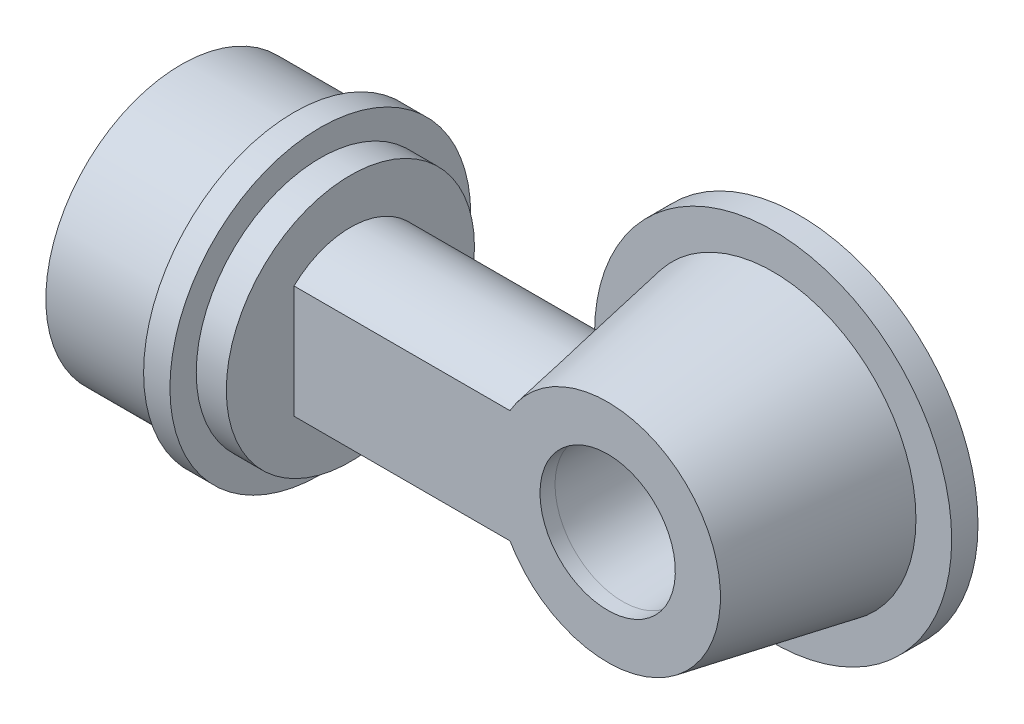
SolidWorks part; units mm, degrees
ref_plane "Front Plane" through (0, 0, 0) normal (0, 0, 1) x (1, 0, 0)
ref_plane "Top Plane" through (0, 0, 0) normal (0, 1, 0) x (1, 0, 0)
ref_plane "Right Plane" through (0, 0, 0) normal (1, 0, 0) x (0, 0, -1)
sketch "Croquis1" plane through (0, 0, 0) normal (1, 0, 0) x (0, 0, -1)
  circle A0 centre (0, 0) radius 18
  circle A1 centre (0, 0) radius 15.5
  dimension "D1" = 36
  dimension "D2" = 2.5
extrude "Saliente-Extruir1" add sketch "Croquis1" along normal blind 15
sketch "Croquis2" plane through (15, 0, 0) normal (1, 0, 0) x (0, 0, -1)
  circle A0 centre (0, 0) radius 20
  circle A1 centre (0, 0) radius 15.5
  circle A2 centre (0, 0) radius 15.5 construction
  dimension "D1" = 40
extrude "Saliente-Extruir2" add sketch "Croquis2" along normal blind 3.5
sketch "Croquis4" plane through (18.5, 0, 0) normal (1, 0, 0) x (0, 0, -1)
  circle A0 centre (0, 0) radius 16.5
  circle A1 centre (0, 0) radius 13.5
  dimension "D1" = 33
  dimension "D2" = 3
extrude "Saliente-Extruir3" add sketch "Croquis4" along normal blind 4
sketch "Croquis5" plane through (22.5, 0, 0) normal (1, 0, 0) x (0, 0, -1)
  circle A0 centre (0, 0) radius 16.5
  circle A1 centre (0, 0) radius 16.5 construction
extrude "Saliente-Extruir4" add sketch "Croquis5" against normal blind 3
sketch "Croquis6" plane through (22.5, 0, 0) normal (1, 0, 0) x (0, 0, -1)
  line L0 (0, 10.5) -> (0, 7.5) construction
  line L4 (-7.5, 7.5) -> (-7.5, -7.5)
  line L6 (7.5, 7.5) -> (7.5, -7.5)
  line L7 (-7.5, 7.5) -> (7.5, -7.5) construction
  line L8 (-7.5, -7.5) -> (7.5, 7.5) construction
  line L9 (0, -7.5) -> (0, -10.5) construction
  line L10 (-5.5, 6.5903) -> (-5.5, -6.5903)
  line L11 (5.5, 6.5903) -> (5.5, -6.5903)
  arc A2 (-7.5, 7.5) -> (7.5, 7.5) centre (0, -0.375) cw
  arc A3 (-7.5, -7.5) -> (7.5, -7.5) centre (0, 0.375) ccw
  arc A4 (-5.5, -6.5903) -> (5.5, -6.5903) centre (0, 0.375) ccw
  arc A5 (-5.5, 6.5903) -> (5.5, 6.5903) centre (0, -0.375) cw
  point P0 (0, 0)
  dimension "D1" = 15
  dimension "D2" = 15
  dimension "D3" = 21
  dimension "D4" = 10.5
  dimension "D5" = 2
extrude "Saliente-Extruir5" add sketch "Croquis6" along normal blind 31
sketch "Croquis7" plane through (0, 0, 7.5) normal (0, 0, 1) x (1, 0, 0)
  line L0 (53.5, 0) -> (77.2121, 0) construction
  line L1 (53.5, 7.5) -> (53.5, -7.5) construction
  circle A0 centre (64.2121, 0) radius 15
  dimension "D1" = 30
ref_plane "Plano1" through (0, 0, -14.5) normal (0, 0, 1) x (1, 0, 0)
sketch "Croquis8" plane through (0, 0, -14.5) normal (0, 0, 1) x (1, 0, 0)
  circle A0 centre (64.2121, 0) radius 19
  dimension "D1" = 38
loft "Recubrir1" add profiles "Croquis7", "Croquis8"
sketch "Croquis9" plane through (0, 0, 7.5) normal (0, 0, 1) x (1, 0, 0)
  circle A0 centre (64.2121, 0) radius 13
  arc A1 (51.2218, -7.5) -> (51.2218, 7.5) centre (64.2121, 0) ccw construction
  dimension "D1" = 2
sketch "Croquis10" plane through (0, 0, -14.5) normal (0, 0, -1) x (-1, 0, 0)
  circle A0 centre (-64.2121, 0) radius 17
  circle A1 centre (-64.2121, 0) radius 19 construction
  dimension "D1" = 2
loft "Cortar-Recubrir1" cut profiles "Croquis9", "Croquis10"
sketch "Croquis11" plane through (22.5, 0, 0) normal (1, 0, 0) x (0, 0, -1)
  line L2 (-5.5, 6.5903) -> (-5.5, -6.5903)
  line L3 (5.5, -6.5903) -> (5.5, 6.5903)
  line L4 (-5.5, 6.5903) -> (-5.5, -6.5903)
  line L5 (5.5, -6.5903) -> (5.5, 6.5903)
  arc A2 (5.5, 6.5903) -> (-5.5, 6.5903) centre (0, -0.375) ccw
  arc A3 (-5.5, -6.5903) -> (5.5, -6.5903) centre (0, 0.375) ccw
  arc A4 (5.5, 6.5903) -> (-5.5, 6.5903) centre (0, -0.375) ccw
  arc A5 (-5.5, -6.5903) -> (5.5, -6.5903) centre (0, 0.375) ccw
  dimension "D1" = 0
extrude "Cortar-Extruir1" cut sketch "Croquis11" against normal blind 13 and the other way blind 41
sketch "Croquis12" plane through (0, 0, 7.5) normal (0, 0, 1) x (1, 0, 0)
  circle A0 centre (64.2121, 0) radius 15
  arc A1 (51.2218, -7.5) -> (51.2218, 7.5) centre (64.2121, 0) ccw construction
extrude "Saliente-Extruir6" add sketch "Croquis12" against normal blind 2
sketch "Croquis14" plane through (0, 0, 5.5) normal (0, 0, -1) x (-1, 0, 0)
  line L0 (-19.5, -6.5903) -> (-19.5, 6.5903) construction
  line L1 (-52.5865, 6.5903) -> (-19.5, 6.5903) construction
  circle A2 centre (-64.2121, 0) radius 11
  dimension "D1" = 22
  dimension "D2" = 44.7121
  dimension "D3" = 6.5903
extrude "Saliente-Extruir7" add sketch "Croquis14" along normal blind 22 draft 2
sketch "Croquis15" plane through (0, 0, -16.5) normal (0, 0, -1) x (-1, 0, 0)
  circle A0 centre (-64.2121, 0) radius 8.2317
  circle A1 centre (-64.2121, 0) radius 10.2317 construction
  dimension "D1" = 2
sketch "Croquis17" plane through (0, 0, 5.5) normal (0, 0, -1) x (-1, 0, 0)
  circle A2 centre (-64.2121, 0) radius 9
  point P0 (0, 0)
  dimension "D1" = 18
loft "Cortar-Recubrir2" cut profiles "Croquis17", "Croquis15"
sketch "Croquis18" plane through (0, 0, 5.5) normal (0, 0, -1) x (-1, 0, 0)
  circle A1 centre (-64.2121, 0) radius 9
  circle A2 centre (-64.2121, 0) radius 9
  dimension "D1" = 0
extrude "Cortar-Extruir2" cut sketch "Croquis18" against normal blind 57
sketch "Croquis19" plane through (0, 0, -16.5) normal (0, 0, -1) x (-1, 0, 0)
  circle A0 centre (-64.2121, 0) radius 10.2317 construction
  circle A1 centre (-64.2121, 0) radius 10.2317
extrude "Saliente-Extruir8" add sketch "Croquis19" against normal blind 2
sketch "Croquis20" plane through (0, 0, -14.5) normal (0, 0, -1) x (-1, 0, 0)
  circle A0 centre (-64.2121, 0) radius 23.75
  circle A1 centre (-64.2121, 0) radius 17 construction
  circle A2 centre (-64.2121, 0) radius 17
  dimension "D1" = 47.5
extrude "Saliente-Extruir9" add sketch "Croquis20" along normal blind 3.5
